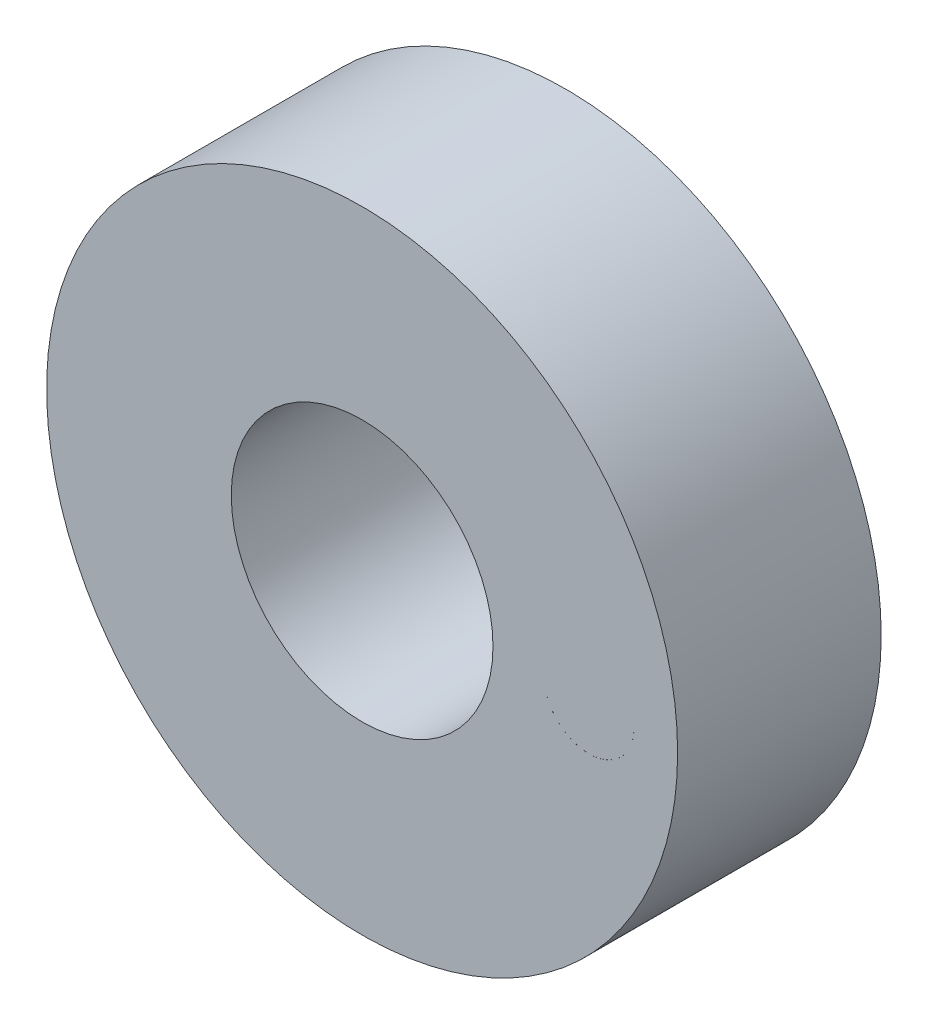
SolidWorks part; units mm, degrees
ref_plane "Front Plane" through (0, 0, 0) normal (0, 0, 1) x (1, 0, 0)
ref_plane "Top Plane" through (0, 0, 0) normal (0, 1, 0) x (1, 0, 0)
ref_plane "Right Plane" through (0, 0, 0) normal (1, 0, 0) x (0, 0, -1)
sketch "Sketch1" plane through (0, 0, 0) normal (0, 0, 1) x (1, 0, 0)
  circle A0 centre (0, 0) radius 10.85
  circle A1 centre (0, 0) radius 4.5
  circle A2 centre (-7.8, 0) radius 1.55
  circle A4 centre (0, 7.8) radius 1.55
  circle A5 centre (7.8, 0) radius 1.55
  circle A6 centre (0, -7.8) radius 1.55
  point P17 (0, 0)
  dimension "D1" = 3.1
  dimension "D2" = 4
extrude "Boss-Extrude1" add sketch "Sketch1" along normal blind 7
sketch "Sketch2" plane through (0, 0, 7) normal (0, 0, 1) x (1, 0, 0)
  circle A0 centre (0, 7.8) radius 1.55
  circle A1 centre (-7.8, 0) radius 1.55
  circle A2 centre (0, -7.8) radius 1.55
  circle A4 centre (7.8, 0.0016) radius 1.55
extrude "Boss-Extrude2" add sketch "Sketch2" against normal blind 3
